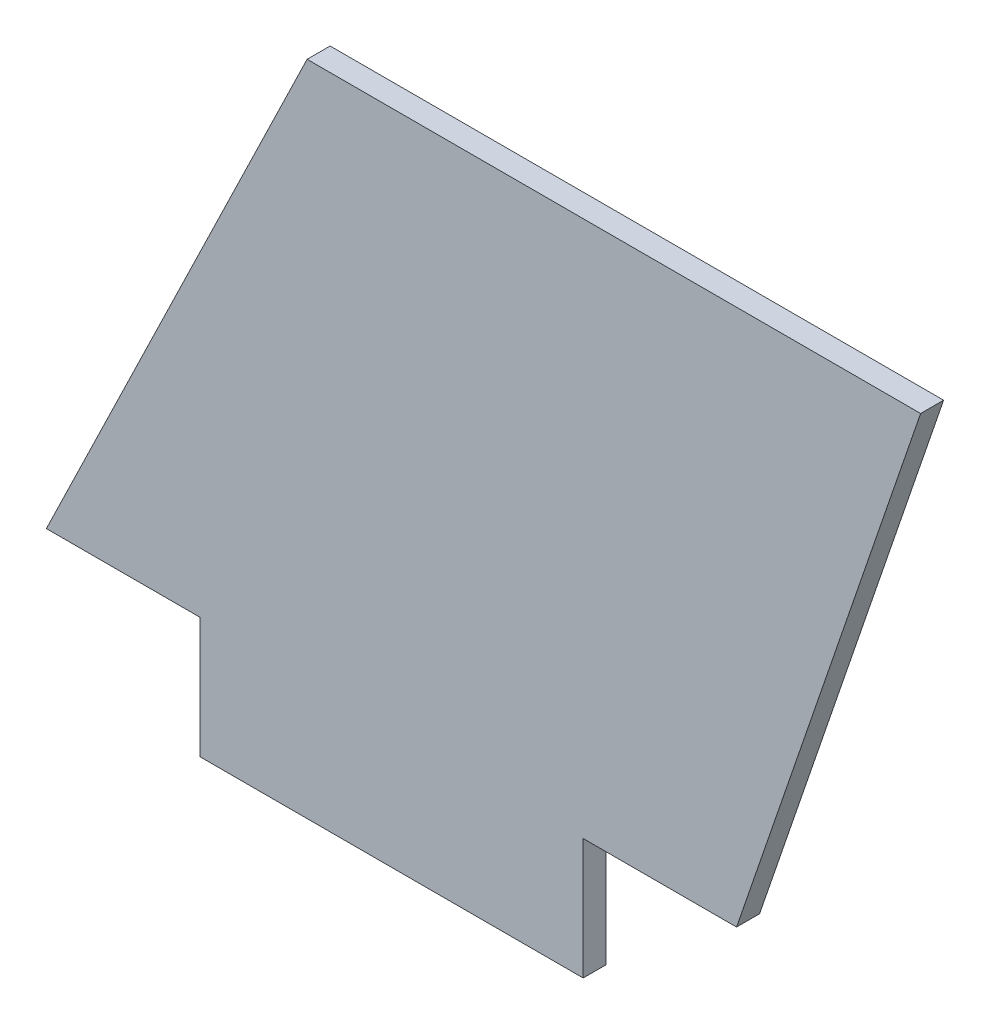
SolidWorks part; units mm, degrees
ref_plane "Front Plane" through (0, 0, 0) normal (0, 0, 1) x (1, 0, 0)
ref_plane "Top Plane" through (0, 0, 0) normal (0, 1, 0) x (1, 0, 0)
ref_plane "Right Plane" through (0, 0, 0) normal (1, 0, 0) x (0, 0, -1)
sketch "Sketch1" plane through (0, 0, 0) normal (0, 0, 1) x (1, 0, 0)
  line L0 (0, 0) -> (10, 0)
  line L1 (10, 0) -> (10, -7.875)
  line L2 (10, -7.875) -> (35, -7.875)
  line L3 (35, -7.875) -> (35, 0)
  line L4 (35, 0) -> (45, 0)
  line L5 (45, 0) -> (57, 35)
  line L6 (57, 35) -> (17, 35)
  line L7 (17, 35) -> (0, 0)
  dimension "D1" = 45
  dimension "D2" = 7.875
  dimension "D3" = 25
  dimension "D4" = 17
  dimension "D5" = 40
  dimension "D6" = 10
  dimension "D7" = 35
extrude "Boss-Extrude1" add sketch "Sketch1" along normal blind 1.5
